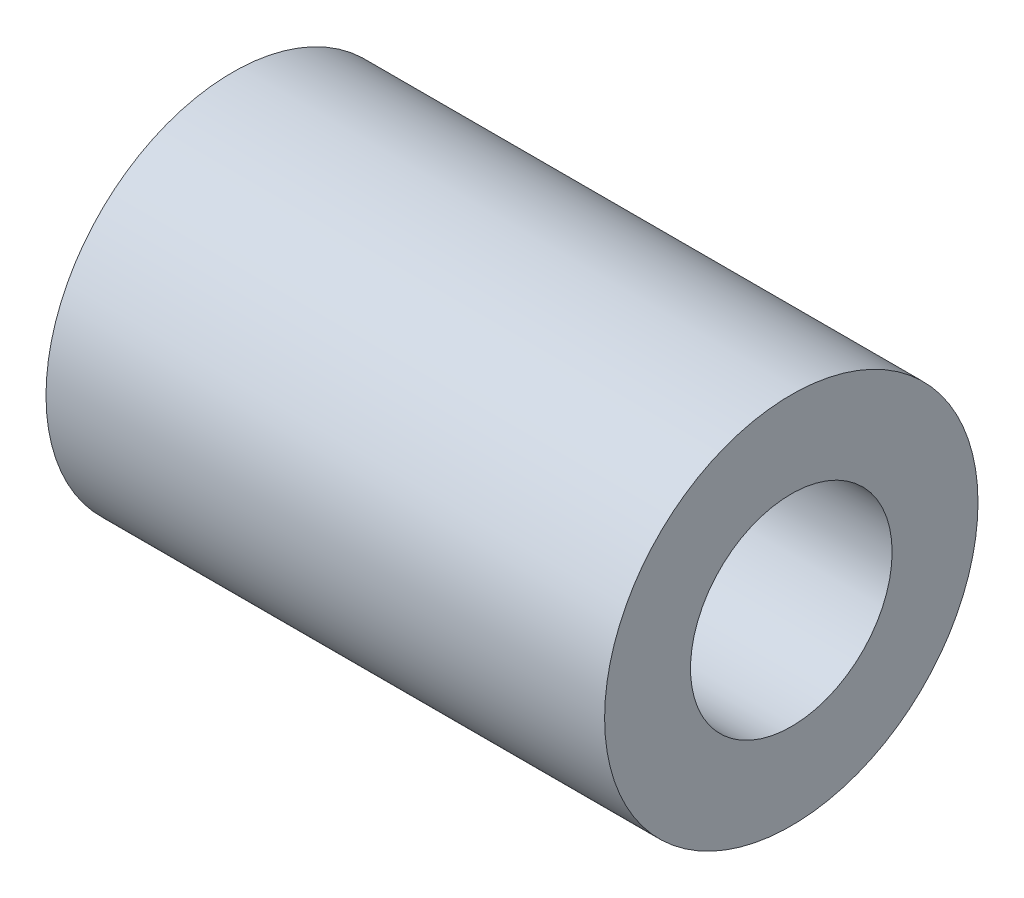
SolidWorks part; units mm, degrees
ref_plane "Plan de face" through (0, 0, 0) normal (0, 0, 1) x (1, 0, 0)
ref_plane "Plan de dessus" through (0, 0, 0) normal (0, 1, 0) x (1, 0, 0)
ref_plane "Plan de droite" through (0, 0, 0) normal (1, 0, 0) x (0, 0, -1)
sketch "Esquisse1" plane through (0, 0, 0) normal (1, 0, 0) x (0, 0, -1)
  circle A0 centre (0, 0) radius 3.429
  circle A1 centre (0, 0) radius 6.35
  dimension "D1" = 6.858
  dimension "D2" = 12.7
extrude "Boss.-Extru.1" add sketch "Esquisse1" against normal blind 19
equation "\"D1@Boss.-Extru.1\"=19mm"
